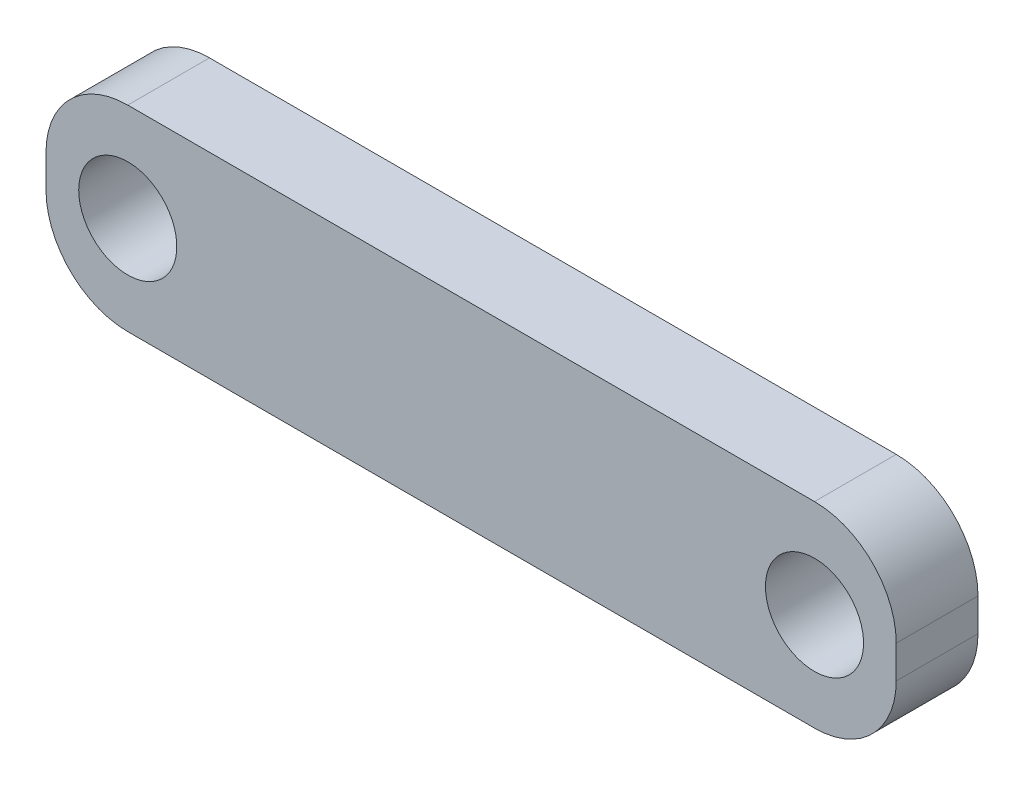
SolidWorks part; units mm, degrees
material "Alliage 1060"
ref_plane "Plan de face" through (0, 0, 0) normal (0, 0, 1) x (1, 0, 0)
ref_plane "Plan de dessus" through (0, 0, 0) normal (0, 1, 0) x (1, 0, 0)
ref_plane "Plan de droite" through (0, 0, 0) normal (1, 0, 0) x (0, 0, -1)
ref_plane "Plan1" through (0, 0, 5) normal (0, 0, 1) x (1, 0, 0)
sketch "Esquisse1" plane through (0, 0, 5) normal (0, 0, 1) x (1, 0, 0)
  line L0 (-26, 1) -> (-26, -1)
  line L1 (-21, -6) -> (21, -6)
  line L2 (26, -1) -> (26, 1)
  line L3 (21, 6) -> (-21, 6)
  line L4 (-21, -6) -> (21, 6) construction
  line L5 (-21, 6) -> (21, -6) construction
  circle A0 centre (21, 0) radius 3
  circle A1 centre (-21, 0) radius 3
  arc A2 (-26, -1) -> (-21, -6) centre (-21, -1) ccw
  arc A3 (21, -6) -> (26, -1) centre (21, -1) ccw
  arc A4 (26, 1) -> (21, 6) centre (21, 1) ccw
  arc A5 (-21, 6) -> (-26, 1) centre (-21, 1) ccw
  dimension "D1" = 6
  dimension "D4" = 5
  dimension "D2" = 52
  dimension "D3" = 12
extrude "Boss.-Extru.1" add sketch "Esquisse1" against normal blind 5
